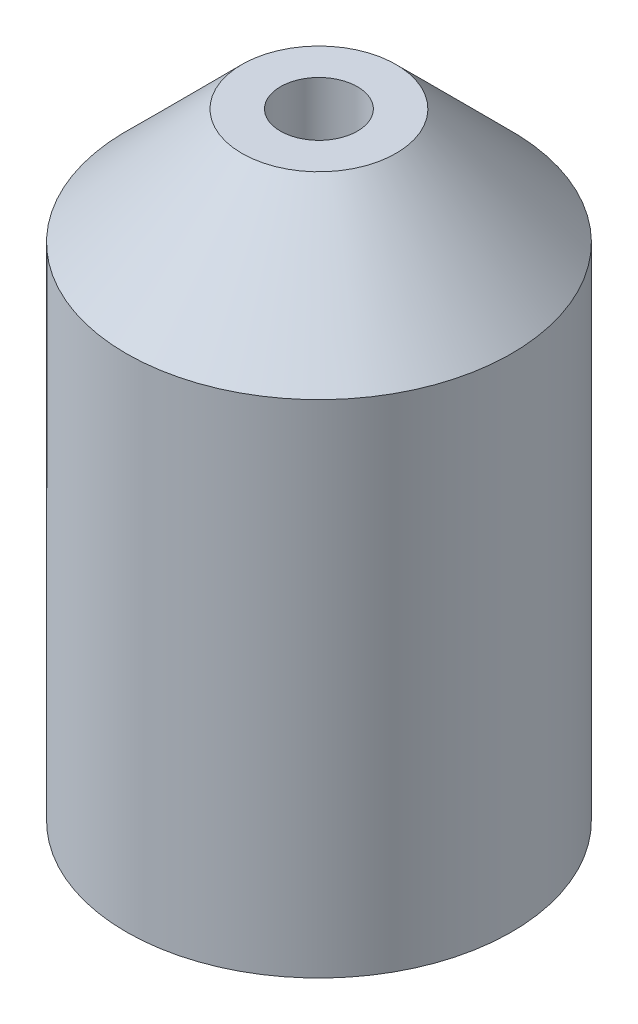
SolidWorks part; units mm, degrees
ref_plane "Front Plane" through (0, 0, 0) normal (0, 0, 1) x (1, 0, 0)
ref_plane "Top Plane" through (0, 0, 0) normal (0, 1, 0) x (1, 0, 0)
ref_plane "Right Plane" through (0, 0, 0) normal (1, 0, 0) x (0, 0, -1)
sketch "Sketch1" plane through (0, 0, 0) normal (0, 1, 0) x (1, 0, 0)
  circle A0 centre (0, 0) radius 5
  dimension "D1" = 10
extrude "Boss-Extrude1" add sketch "Sketch1" along normal blind 16 contours A0
chamfer "Chamfer1" distance 3 angle 45 1 edges at (0, 16, 5)
sketch "Sketch2" plane through (0, 16, 0) normal (0, 1, 0) x (1, 0, 0)
  circle A0 centre (0, 0) radius 1
  dimension "D1" = 2
extrude "Cut-Extrude1" cut sketch "Sketch2" against normal blind 7
sketch "Sketch3" plane through (0, 0, 0) normal (0, -1, 0) x (1, 0, 0)
  line L1 (-2.1651, 3.75) -> (-4.3301, 0)
  line L2 (-4.3301, 0) -> (-2.1651, -3.75)
  line L3 (-2.1651, -3.75) -> (2.1651, -3.75)
  line L4 (2.1651, -3.75) -> (4.3301, 0)
  line L5 (4.3301, 0) -> (2.1651, 3.75)
  line L6 (2.1651, 3.75) -> (-2.1651, 3.75)
  circle A0 centre (0, 0) radius 3.75 construction
  dimension "D1" = 7.5
extrude "Cut-Extrude2" cut sketch "Sketch3" against normal blind 7
chamfer "Chamfer2" distance 2.5 angle 45 6 edges at (3.2476, 7, 1.875) (3.2476, 7, -1.875) (0, 7, -3.75) (-3.2476, 7, -1.875) (-3.2476, 7, 1.875) (0, 7, 3.75)
